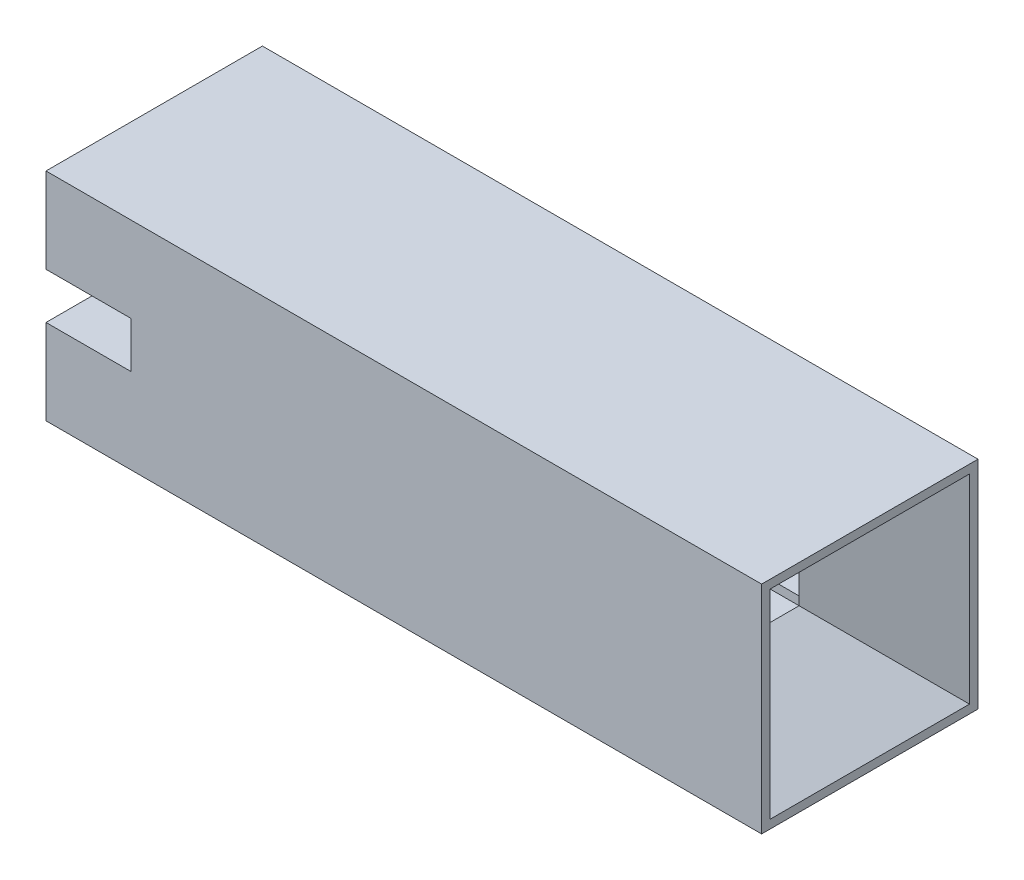
SolidWorks part; units mm, degrees
material "ABS PC"
ref_plane "Front Plane" through (0, 0, 0) normal (0, 0, 1) x (1, 0, 0)
ref_plane "Top Plane" through (0, 0, 0) normal (0, 1, 0) x (1, 0, 0)
ref_plane "Right Plane" through (0, 0, 0) normal (1, 0, 0) x (0, 0, -1)
sketch "Sketch1" plane through (0, 0, 0) normal (0, 0, 1) x (1, 0, 0)
  line L1 (0, 0) -> (8.4, 0)
  line L2 (0, 0) -> (0, 2.54)
  line L3 (0, 2.54) -> (8.4, 2.54)
  line L4 (8.4, 0) -> (8.4, 2.54)
  dimension "D1" = 2.54
  dimension "D2" = 8.4
extrude "Boss-Extrude1" add sketch "Sketch1" along normal blind 2.54
sketch "Sketch2" plane through (8.4, 0, 0) normal (1, 0, 0) x (0, 0, -1)
  line L0 (-2.54, 2.54) -> (0, 2.54) construction
  line L1 (-1.64, 1.64) -> (-0.9, 1.64)
  line L2 (-1.64, 1.64) -> (-1.64, 0.9)
  line L3 (-1.64, 0.9) -> (-0.9, 0.9)
  line L4 (-0.9, 1.64) -> (-0.9, 0.9)
  line L5 (-2.54, 0) -> (0, 0) construction
  line L6 (-2.54, 0) -> (-2.54, 2.54) construction
  dimension "D1" = 0.9
  dimension "D2" = 0.9
  dimension "D3" = 0.9
  dimension "D4" = 0.74
extrude "Cut-Extrude1" cut sketch "Sketch2" against normal up to next
chamfer "Chamfer2" distance 0.8 distance2 1.2 4 edges at (8.4, 1.27, 1.64) (8.4, 0.9, 1.27) (8.4, 1.27, 0.9) (8.4, 1.64, 1.27)
sketch "Sketch3" plane through (0, 0, 0) normal (-1, 0, 0) x (0, 0, 1)
  line L0 (0, 2.54) -> (0, 0) construction
  line L1 (0, 1.54) -> (2.54, 1.54)
  line L2 (0, 1.54) -> (0, 1)
  line L3 (0, 1) -> (2.54, 1)
  line L4 (2.54, 1.54) -> (2.54, 1)
  line L5 (2.54, 2.54) -> (2.54, 0) construction
  line L6 (2.54, 0) -> (0, 0) construction
  line L7 (2.54, 2.54) -> (0, 2.54) construction
  dimension "D1" = 1
  dimension "D2" = 1
extrude "Cut-Extrude2" cut sketch "Sketch3" against normal blind 1
sketch "Sketch5" plane through (1, 0, 0) normal (-1, 0, 0) x (0, 0, 1)
  line L0 (1.64, 1) -> (2.54, 1) construction
  line L1 (2.14, 1) -> (0.4, 1)
  line L2 (2.14, 1) -> (2.14, 1.54)
  line L3 (2.14, 1.54) -> (0.4, 1.54)
  line L4 (0.4, 1) -> (0.4, 1.54)
  line L5 (0.9, 1.54) -> (0, 1.54) construction
  line L6 (0, 1.54) -> (0, 1) construction
  line L7 (2.54, 1) -> (2.54, 1.54) construction
  dimension "D1" = 0.4
  dimension "D2" = 0.4
extrude "Cut-Extrude4" cut sketch "Sketch5" against normal up to vertex (4.34 mm away)
